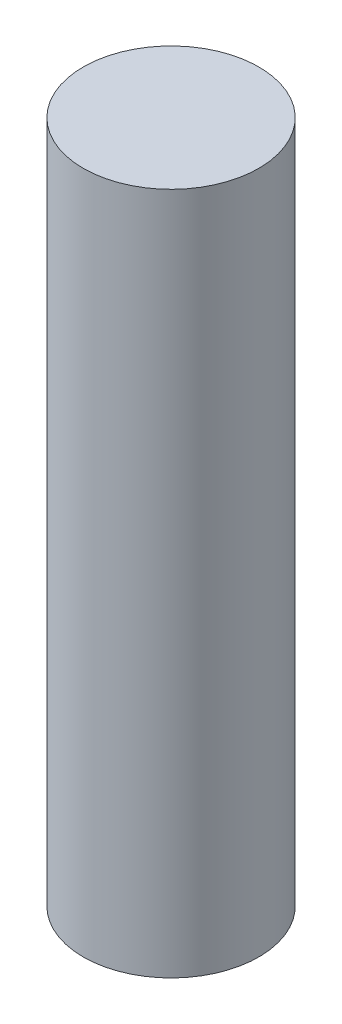
SolidWorks part; units mm, degrees
ref_plane "Front Plane" through (0, 0, 0) normal (0, 0, 1) x (1, 0, 0)
ref_plane "Top Plane" through (0, 0, 0) normal (0, 1, 0) x (1, 0, 0)
ref_plane "Right Plane" through (0, 0, 0) normal (1, 0, 0) x (0, 0, -1)
sketch "Sketch2" plane through (0, 0, 0) normal (0, 1, 0) x (1, 0, 0)
  circle A0 centre (0, 0) radius 9
  dimension "D1" = 18
extrude "Boss-Extrude1" add sketch "Sketch2" along normal blind 70
sketch "Sketch3" plane through (0, 0, 0) normal (0, -1, 0) x (1, 0, 0)
  circle A0 centre (0, 0) radius 7.5
  circle A1 centre (0, 0) radius 9 construction
  dimension "D1" = 1.5
extrude "Cut-Extrude1" cut sketch "Sketch3" against normal blind 1
sketch "Sketch4" plane through (0, 1, 0) normal (0, -1, 0) x (1, 0, 0)
  circle A0 centre (0, 0) radius 1.5
  dimension "D1" = 3
extrude "Cut-Extrude2" cut sketch "Sketch4" against normal blind 50
chamfer "Chamfer1" distance 1 angle 60 1 edges at (0, 1, -1.5)
